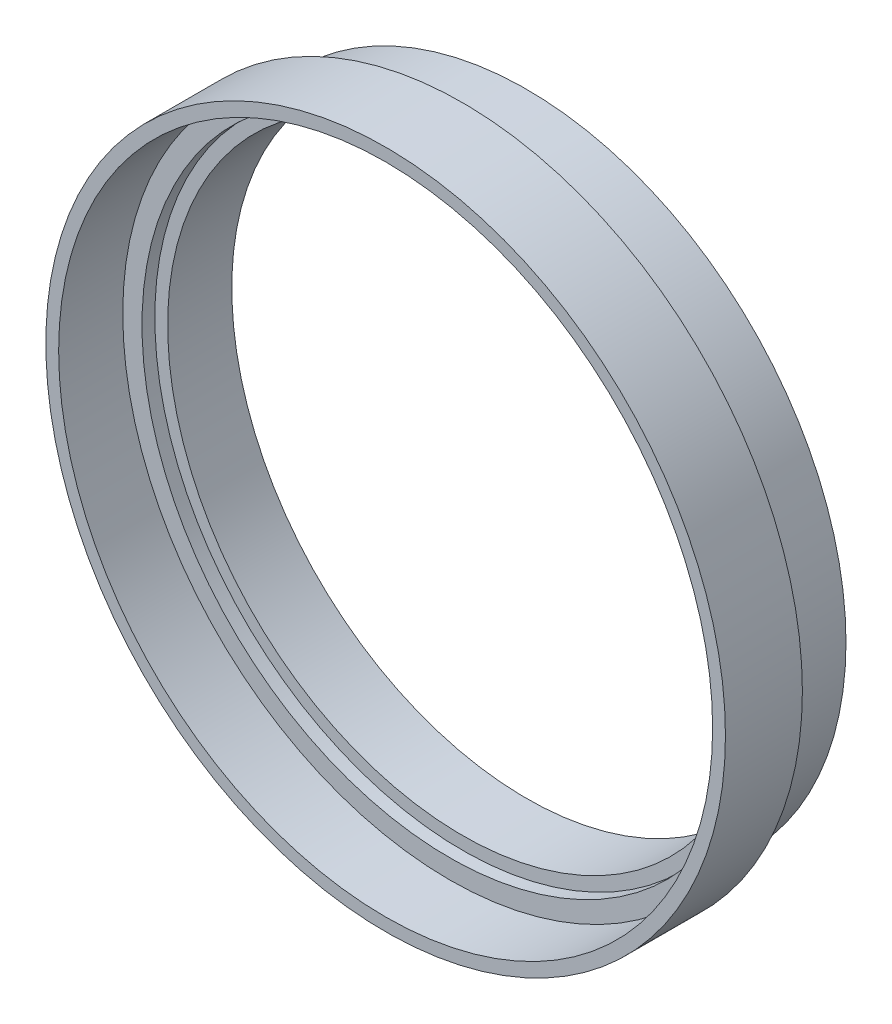
SolidWorks part; units mm, degrees
ref_plane "前视基准面" through (0, 0, 0) normal (0, 0, 1) x (1, 0, 0)
ref_plane "上视基准面" through (0, 0, 0) normal (0, 1, 0) x (1, 0, 0)
ref_plane "右视基准面" through (0, 0, 0) normal (1, 0, 0) x (0, 0, -1)
sketch "草图1" plane through (0, 0, 0) normal (0, 0, 1) x (1, 0, 0)
  circle A0 centre (0, 0) radius 24.9
  circle A1 centre (0, 0) radius 23
  dimension "D1" = 49.8
  dimension "D2" = 46
extrude "凸台-拉伸1" add sketch "草图1" along normal blind 5
sketch "草图2" plane through (0, 0, 5) normal (0, 0, 1) x (1, 0, 0)
  circle A0 centre (0, 0) radius 26.5
  circle A1 centre (0, 0) radius 24
  dimension "D1" = 53
  dimension "D2" = 48
extrude "凸台-拉伸2" add sketch "草图2" along normal blind 1
sketch "草图3" plane through (0, 0, 6) normal (0, 0, 1) x (1, 0, 0)
  circle A0 centre (0, 0) radius 26.5
  circle A1 centre (0, 0) radius 25.5
  dimension "D1" = 51
  dimension "D2" = 53
extrude "凸台-拉伸3" add sketch "草图3" along normal blind 5
